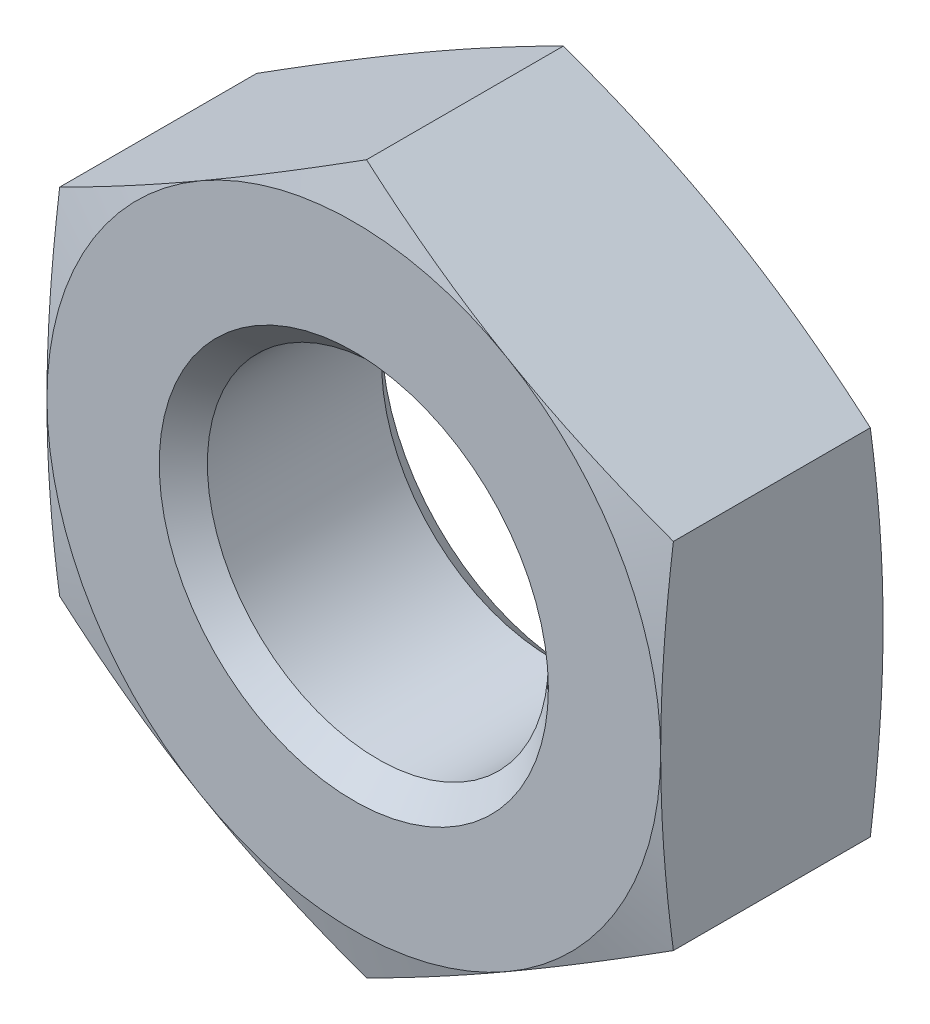
SolidWorks part; units mm, degrees
ref_plane "Front Plane" through (0, 0, 0) normal (0, 0, 1) x (1, 0, 0)
ref_plane "Top Plane" through (0, 0, 0) normal (0, 1, 0) x (1, 0, 0)
ref_plane "Right Plane" through (0, 0, 0) normal (1, 0, 0) x (0, 0, -1)
ref_plane "Plane1" through (0, 0, 0) normal (1, 0, 0) x (0, 0, -1)
sketch "Sketch1" plane through (0, 0, 0) normal (1, 0, 0) x (0, 0, -1)
  line L0 (0, 0) -> (0, 8.763)
  line L1 (0, 8.763) -> (0.4696, 10.5156)
  line L2 (0.4696, 10.5156) -> (5.8804, 10.5156)
  line L3 (5.8804, 10.5156) -> (6.35, 8.763)
  line L4 (6.35, 8.763) -> (6.35, 0)
  line L5 (6.35, 0) -> (0, 0)
  line L6 (6.35, 0) -> (0, 0) construction
revolve "Revolve1" add sketch "Sketch1" angle 360 about L6
ref_plane "Plane2" through (0, 0, 0) normal (0, 0, 1) x (1, 0, 0)
sketch "Sketch2" plane through (0, 0, 0) normal (0, 0, 1) x (1, 0, 0)
  line L0 (-17.526, -17.526) -> (17.526, -17.526)
  line L1 (17.526, -17.526) -> (17.526, 17.526)
  line L2 (17.526, 17.526) -> (-17.526, 17.526)
  line L3 (-17.526, 17.526) -> (-17.526, -17.526)
  line L4 (-8.763, -5.0593) -> (0, -10.1186)
  line L5 (0, -10.1186) -> (8.763, -5.0593)
  line L6 (8.763, -5.0593) -> (8.763, 5.0593)
  line L7 (8.763, 5.0593) -> (0, 10.1186)
  line L8 (0, 10.1186) -> (-8.763, 5.0593)
  line L9 (-8.763, 5.0593) -> (-8.763, -5.0593)
extrude "Cut-Extrude1" cut sketch "Sketch2" against normal blind 6.35
ref_plane "Plane3" through (0, 0, 0) normal (1, 0, 0) x (0, 0, -1)
sketch "Sketch3" plane through (0, 0, 0) normal (1, 0, 0) x (0, 0, -1)
  line L0 (0, 0) -> (0, 5.5563)
  line L1 (0, 5.5563) -> (0.6871, 4.8692)
  line L2 (0.6871, 4.8692) -> (5.6629, 4.8692)
  line L3 (5.6629, 4.8692) -> (6.35, 5.5563)
  line L4 (6.35, 5.5563) -> (6.35, 0)
  line L5 (6.35, 0) -> (0, 0)
  line L6 (6.35, 0) -> (0, 0) construction
revolve "Cut-Revolve1" cut sketch "Sketch3" angle 360 about L6
